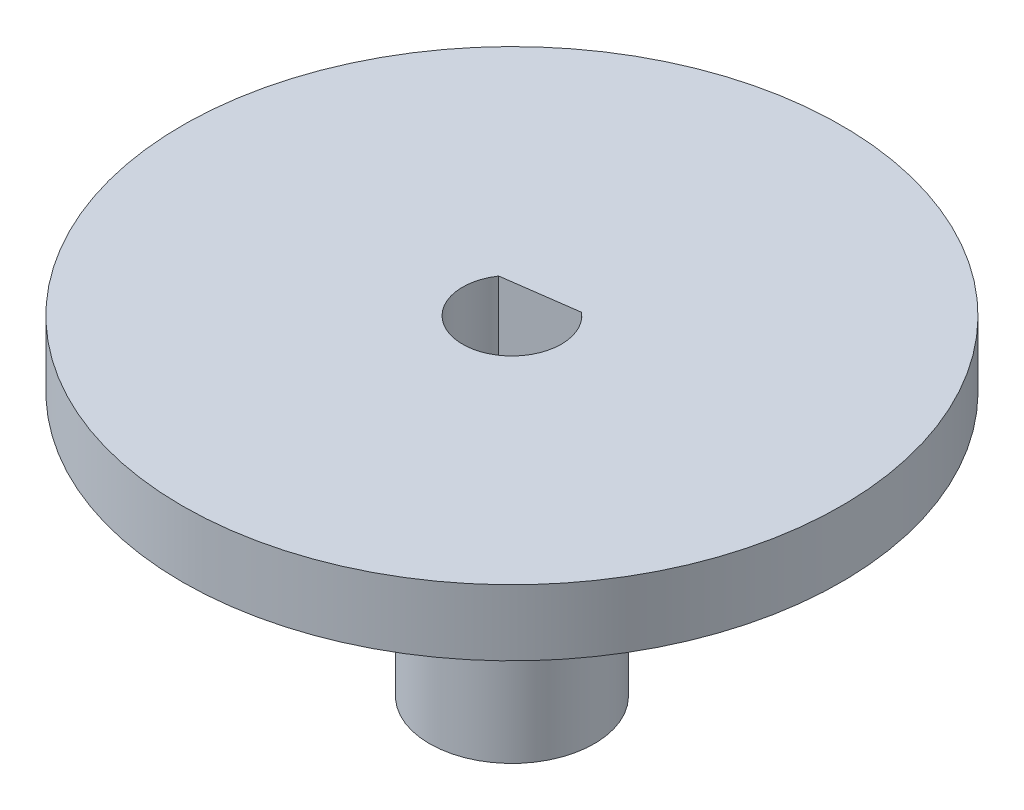
SolidWorks part; units mm, degrees
ref_plane "Front Plane" through (0, 0, 0) normal (0, 0, 1) x (1, 0, 0)
ref_plane "Top Plane" through (0, 0, 0) normal (0, 1, 0) x (1, 0, 0)
ref_plane "Right Plane" through (0, 0, 0) normal (1, 0, 0) x (0, 0, -1)
sketch "Sketch1" plane through (0, 0, 0) normal (0, 1, 0) x (1, 0, 0)
  line L0 (-1.2424, 0.8404) -> (0.9688, 1.1451)
  line L1 (-1.2424, 0.8404) -> (0.9688, 1.1451)
  circle A0 centre (0, 0) radius 1.5
  arc A1 (0.9688, 1.1451) -> (-1.2424, 0.8404) centre (0, 0) cw
  circle A2 centre (0, 0) radius 2.5
  dimension "D3" = 3
  dimension "D5" = 1
  dimension "D1" = 1.0022
  dimension "D2" = 2.2321
  dimension "D4" = 0.9688
extrude "Boss-Extrude1" add sketch "Sketch1" along normal blind 10
sketch "Sketch3" plane through (0, 10, 0) normal (0, 1, 0) x (1, 0, 0)
  circle A0 centre (0, 0) radius 2.5
  circle A1 centre (0, 0) radius 10
  dimension "D1" = 7.5
extrude "Boss-Extrude2" add sketch "Sketch3" against normal blind 2
